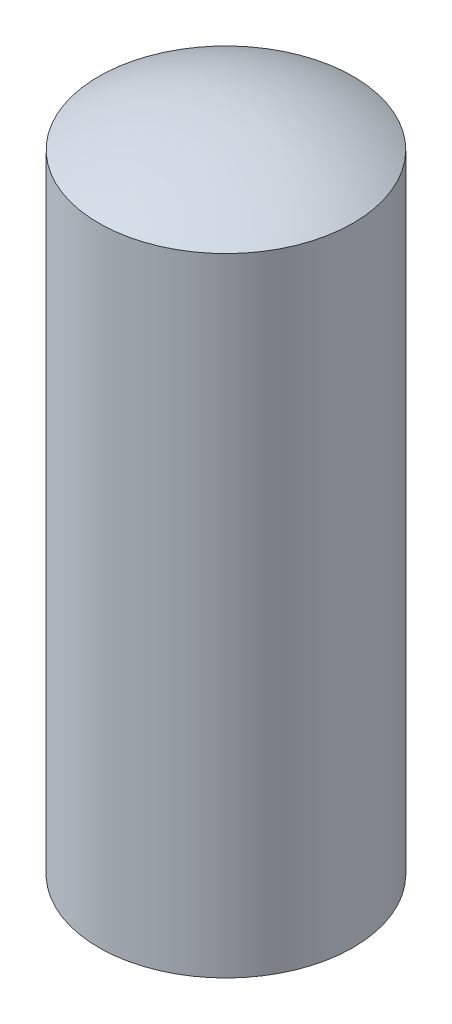
SolidWorks part; units mm, degrees
ref_plane "Plan de face" through (0, 0, 0) normal (0, 0, 1) x (1, 0, 0)
ref_plane "Plan de dessus" through (0, 0, 0) normal (0, 1, 0) x (1, 0, 0)
ref_plane "Plan de droite" through (0, 0, 0) normal (1, 0, 0) x (0, 0, -1)
sketch "Esquisse1" plane through (0, 0, 0) normal (0, 0, 1) x (1, 0, 0)
  line L0 (0, 0) -> (0, 3.9)
  line L1 (0, 3.9) -> (0.75, 3.9) construction
  line L2 (0.75, 3.9) -> (0.75, 0) construction
  line L3 (0.75, 0) -> (0, 0)
  line L4 (0.75, 3.7) -> (0.75, 0)
  arc A0 (0, 3.9) -> (0.75, 3.7) centre (0, 2.3938) cw
  dimension "D1" = 3.9
  dimension "D2" = 0.75
  dimension "D3" = 0.2
revolve "Révolution1" add sketch "Esquisse1" angle 360 about L0
